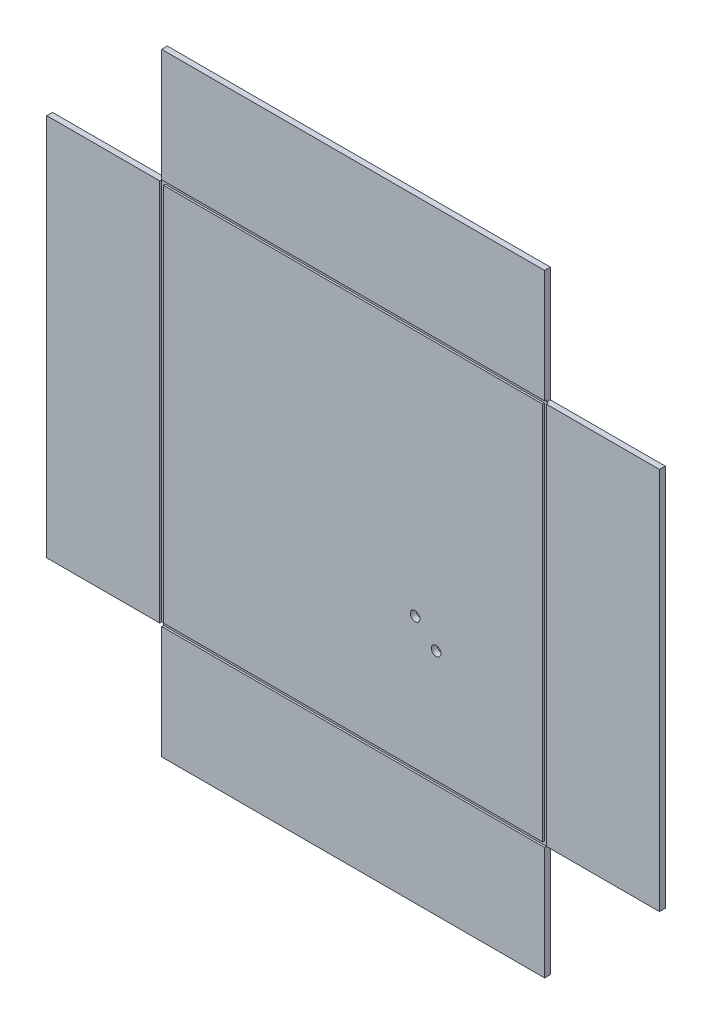
SolidWorks part; units mm, degrees
ref_plane "Plan de face" through (0, 0, 0) normal (0, 0, 1) x (1, 0, 0)
ref_plane "Plan de dessus" through (0, 0, 0) normal (0, 1, 0) x (1, 0, 0)
ref_plane "Plan de droite" through (0, 0, 0) normal (1, 0, 0) x (0, 0, -1)
sketch "Esquisse1" plane through (0, 0, 0) normal (0, 0, 1) x (1, 0, 0)
  line L1 (-160, 160) -> (160, 160)
  line L2 (-160, 160) -> (-160, -160)
  line L3 (-160, -160) -> (160, -160)
  line L4 (160, 160) -> (160, -160)
  point P7 (-141.0206, 7.2982)
  dimension "D1" = 320
  dimension "D2" = 320
  dimension "D3" = 160
  dimension "D4" = 160
extrude "Boss.-Extru.1" add sketch "Esquisse1" along normal blind 3
sketch "Esquisse2" plane through (0, 0, 3) normal (0, 0, 1) x (1, 0, 0)
  line L0 (100, -160) -> (160, -160)
  line L1 (-160, -160) -> (-100, -160)
  line L2 (-160, -160) -> (-160, -100)
  line L3 (-160, -100) -> (-100, -100)
  line L4 (-100, -160) -> (-100, -100)
  line L5 (100, -160) -> (100, -100)
  line L6 (100, -100) -> (160, -100)
  line L7 (160, -160) -> (160, -100)
  line L8 (100, 100) -> (160, 100)
  line L9 (100, 100) -> (100, 160)
  line L10 (100, 160) -> (160, 160)
  line L11 (160, 100) -> (160, 160)
  line L12 (-160, 100) -> (-100, 100)
  line L13 (-160, 100) -> (-160, 160)
  line L14 (-160, 160) -> (-100, 160)
  line L15 (-100, 100) -> (-100, 160)
  dimension "D1" = 100
  dimension "D2" = 100
  dimension "D3" = 2
  dimension "D4" = 2
extrude "Enlèv. mat.-Extru.1" cut sketch "Esquisse2" against normal up to next
sketch "Esquisse3" plane through (0, 0, 3) normal (0, 0, 1) x (1, 0, 0)
  line L0 (-101, 101) -> (101, 101)
  line L1 (-100, 100) -> (100, 100) construction
  line L2 (-100, 100) -> (-100, -100) construction
  line L3 (-100, -100) -> (100, -100) construction
  line L4 (100, 100) -> (100, -100) construction
  line L5 (101, 101) -> (101, -101)
  line L6 (-101, -101) -> (101, -101)
  line L7 (-101, 101) -> (-101, -101)
  line L8 (-99, 99) -> (99, 99)
  line L9 (99, 99) -> (99, -99)
  line L10 (-99, -99) -> (99, -99)
  line L11 (-99, 99) -> (-99, -99)
  dimension "D1" = 1
  dimension "D2" = 1
extrude "Enlèv. mat.-Extru.2" cut sketch "Esquisse3" against normal blind 1
hole_wizard "Diamètre du perçage Ø5.0 (5)1" positions "Esquisse4" profile "Esquisse5" hole size "Ø5.0" standard "Ansi Metric" end condition up to next
sketch "Esquisse4" plane through (0, 0, 3) normal (0, 0, 1) x (1, 0, 0)
  line L0 (32.35, -30.1668) -> (43.3203, -40.3968) construction
  line L1 (43.3203, -40.3968) -> (0, 0) construction
  line L3 (0, 0) -> (58.614, 0) construction
  point P0 (32.35, -30.1668)
  point P2 (43.3203, -40.3968)
  dimension "D1" = 15
  dimension "D2" = 44.233
  dimension "D3" = 43
sketch "Esquisse5" plane through (32.35, -30.1668, 3) normal (1, 0, 0) x (0, -1, 0)
  line L0 (0, 0) -> (0, 3)
  line L1 (0, 3) -> (2.5, 3)
  line L2 (2.5, 3) -> (2.5, 0)
  line L5 (2.5, 0) -> (0, 0)
  line L11 (0, -6.35) -> (0, 107.95) construction
  dimension "Diamètre du perçage jusqu'au prochain" = 5
  dimension "Profondeur du perçage jusqu'au prochain" = 3
